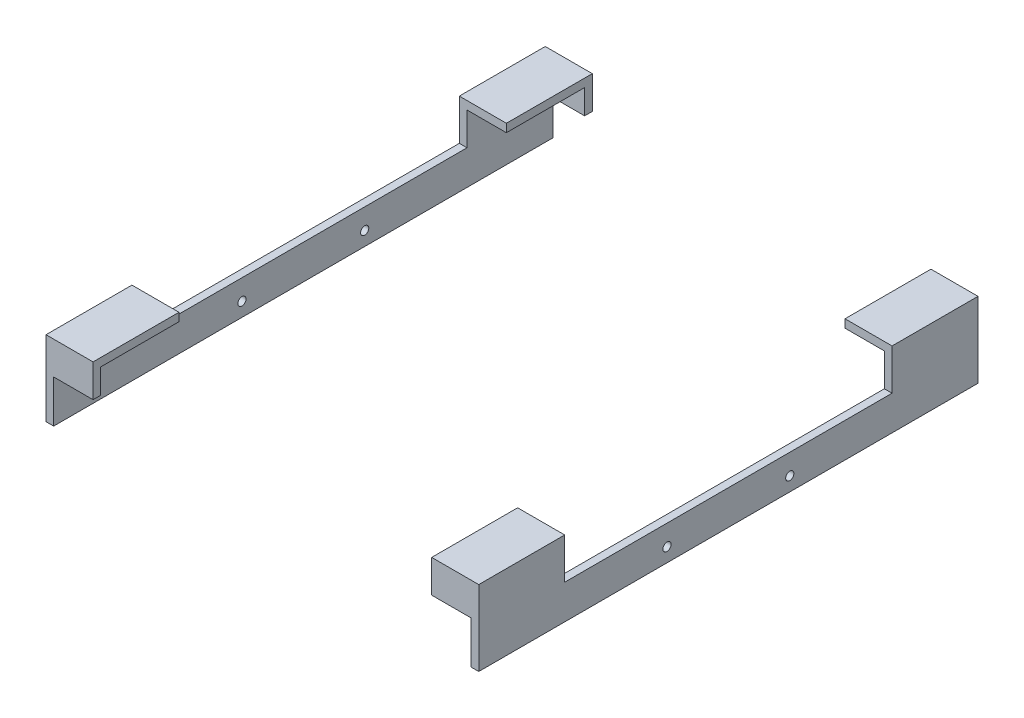
SolidWorks part; units mm, degrees
ref_plane "Front Plane" through (0, 0, 0) normal (0, 0, 1) x (1, 0, 0)
ref_plane "Top Plane" through (0, 0, 0) normal (0, 1, 0) x (1, 0, 0)
ref_plane "Right Plane" through (0, 0, 0) normal (1, 0, 0) x (0, 0, -1)
sketch "Sketch2" plane through (0, 0, 0) normal (0, 0, 1) x (1, 0, 0)
  line L0 (-129.54, 0) -> (-129.54, 45.72)
  line L1 (-129.54, 45.72) -> (-105.0925, 45.72)
  line L2 (-105.0925, 45.72) -> (-105.0925, 50.8)
  line L3 (-105.0925, 50.8) -> (-134.3025, 50.8)
  line L4 (-134.3025, 50.8) -> (-134.3025, 0)
  line L5 (-134.3025, 0) -> (-129.54, 0)
  line L6 (0, 0) -> (0, 130.4972) construction
  line L7 (105.0925, 45.72) -> (105.0925, 50.8)
  line L8 (129.54, 45.72) -> (105.0925, 45.72)
  line L9 (105.0925, 50.8) -> (134.3025, 50.8)
  line L10 (134.3025, 50.8) -> (134.3025, 0)
  line L11 (129.54, 0) -> (129.54, 45.72)
  line L12 (134.3025, 0) -> (129.54, 0)
  dimension "D1" = 129.54
  dimension "D2" = 50.8
  dimension "D3" = 45.72
  dimension "D4" = 4.7625
  dimension "D5" = 29.21
  dimension "D6" = 45.72
extrude "Boss-Extrude1" add sketch "Sketch2" along normal blind 154.94 and the other way blind 154.94
sketch "Sketch3" plane through (0, 0, 154.94) normal (0, 0, 1) x (1, 0, 0)
  line L0 (-105.0925, 50.8) -> (-134.3025, 50.8) construction
  line L1 (-105.0925, 50.8) -> (-134.3025, 50.8)
  line L2 (-134.3025, 50.8) -> (-134.3025, 30.48)
  line L3 (-134.3025, 50.8) -> (-134.3025, 0) construction
  line L4 (-134.3025, 30.48) -> (-105.0925, 30.48)
  line L5 (-105.0925, 30.48) -> (-105.0925, 50.8)
  line L6 (134.3025, 50.8) -> (105.0925, 50.8) construction
  line L7 (134.3025, 50.8) -> (105.0925, 50.8)
  line L8 (105.0925, 50.8) -> (105.0925, 30.48)
  line L9 (105.0925, 30.48) -> (134.3025, 30.48)
  line L10 (134.3025, 0) -> (134.3025, 50.8) construction
  line L11 (134.3025, 30.48) -> (134.3025, 50.8)
  dimension "D1" = 20.32
  dimension "D2" = 20.32
extrude "Boss-Extrude2" add sketch "Sketch3" against normal blind 4.7625
sketch "Sketch4" plane through (0, 0, -154.94) normal (0, 0, -1) x (-1, 0, 0)
  line L0 (105.0925, 50.8) -> (134.3025, 50.8) construction
  line L1 (-134.3025, 50.8) -> (-105.0925, 50.8) construction
  line L2 (105.0925, 50.8) -> (134.3025, 50.8)
  line L3 (-134.3025, 50.8) -> (-105.0925, 50.8)
  line L4 (-105.0925, 50.8) -> (-105.0925, 30.48)
  line L5 (-105.0925, 30.48) -> (-134.3025, 30.48)
  line L6 (-134.3025, 0) -> (-134.3025, 50.8) construction
  line L7 (-134.3025, 30.48) -> (-134.3025, 50.8)
  line L8 (105.0925, 50.8) -> (105.0925, 30.48)
  line L9 (105.0925, 30.48) -> (134.3025, 30.48)
  line L10 (134.3025, 50.8) -> (134.3025, 0) construction
  line L11 (134.3025, 30.48) -> (134.3025, 50.8)
extrude "Boss-Extrude3" add sketch "Sketch4" against normal blind 4.7625
sketch "Sketch5" plane through (0, 0, 0) normal (0, 0, 1) x (1, 0, 0)
  line L0 (134.3025, 50.8) -> (105.0925, 50.8) construction
  line L1 (-105.0925, 50.8) -> (-134.3025, 50.8) construction
  line L2 (134.3025, 50.8) -> (105.0925, 50.8)
  line L3 (-105.0925, 50.8) -> (-134.3025, 50.8)
  line L4 (-134.3025, 50.8) -> (-134.3025, 25.4)
  line L5 (-134.3025, 50.8) -> (-134.3025, 0) construction
  line L6 (-134.3025, 25.4) -> (-105.0925, 25.4)
  line L7 (-105.0925, 25.4) -> (-105.0925, 50.8)
  line L8 (105.0925, 50.8) -> (105.0925, 25.4)
  line L9 (105.0925, 25.4) -> (134.3025, 25.4)
  line L10 (134.3025, 0) -> (134.3025, 50.8) construction
  line L11 (134.3025, 25.4) -> (134.3025, 50.8)
extrude "Cut-Extrude1" cut sketch "Sketch5" against normal blind 101.6 and the other way blind 101.6
split "Split1" bodies to split 108 107 resulting bodies 111 112
sketch "Sketch6" plane through (-134.3025, 0, 0) normal (-1, 0, 0) x (0, 0, 1)
  line L0 (-154.94, 0) -> (154.94, 0) construction
  line L5 (-101.6, 25.4) -> (101.6, 0) construction
  line L6 (-101.6, 0) -> (101.6, 25.4) construction
  line L7 (0, 25.4) -> (0, 0) construction
  line L8 (-101.6, 12.7) -> (101.6, 12.7) construction
  line L9 (101.6, 25.4) -> (101.6, 0) construction
  line L10 (-101.6, 25.4) -> (-101.6, 0) construction
  circle A0 centre (38.1, 12.7) radius 2.54
  circle A1 centre (-38.1, 12.7) radius 2.54
  point P4 (0, 12.7)
  dimension "D1" = 5.08
extrude "Cut-Extrude3" cut sketch "Sketch6" against normal through all
sketch "Sketch7" plane through (134.3025, 0, 0) normal (1, 0, 0) x (0, 0, -1)
  line L0 (154.94, 0) -> (154.94, 50.8) construction
  line L1 (-154.94, 0) -> (154.94, 0)
  line L2 (-154.94, 0) -> (-154.94, 4.0503)
  line L3 (-154.94, 4.0503) -> (154.94, 4.0503)
  line L4 (154.94, 0) -> (154.94, 4.0503)
  line L5 (-154.94, 0) -> (154.94, 4.0503) construction
  line L6 (-154.94, 4.0503) -> (154.94, 0) construction
  point P4 (0, 2.0252)
extrude "Cut-Extrude4" cut sketch "Sketch7" against normal through all
